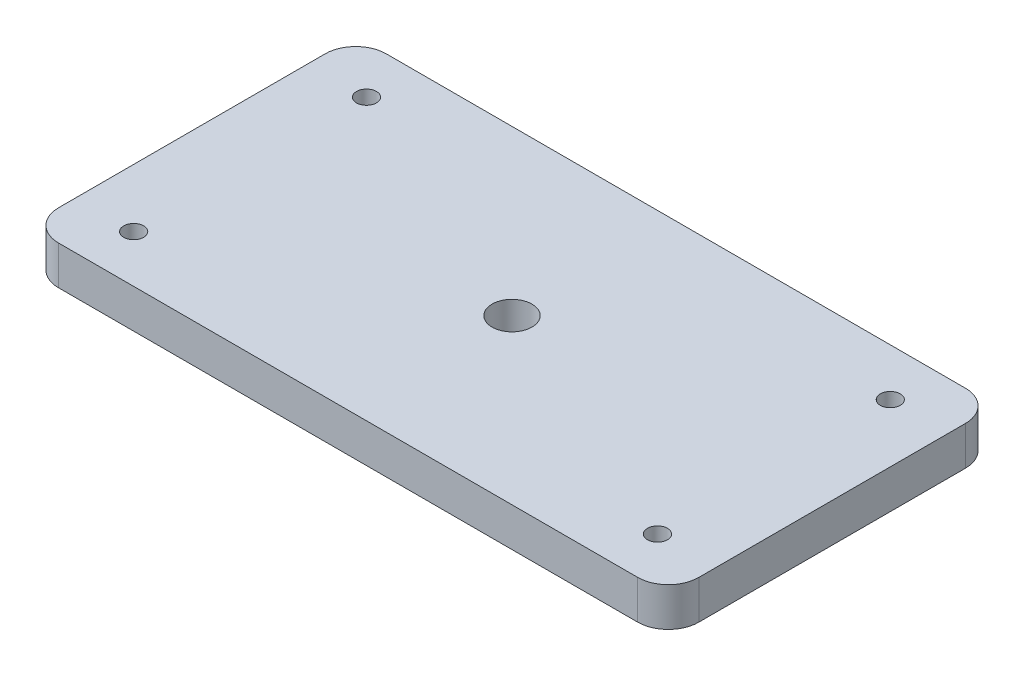
SolidWorks part; units mm, degrees
ref_plane "Front Plane" through (0, 0, 0) normal (0, 0, 1) x (1, 0, 0)
ref_plane "Top Plane" through (0, 0, 0) normal (0, 1, 0) x (1, 0, 0)
ref_plane "Right Plane" through (0, 0, 0) normal (1, 0, 0) x (0, 0, -1)
sketch "Sketch1" plane through (0, 0, 0) normal (0, 1, 0) x (1, 0, 0)
  line L1 (0, 53.63) -> (104.78, 53.63)
  line L2 (0, 53.63) -> (0, 0)
  line L3 (0, 0) -> (104.78, 0)
  line L4 (104.78, 53.63) -> (104.78, 0)
  dimension "dim1" = 104.78
  dimension "dim2" = 53.63
extrude "Boss-Extrude1" add sketch "Sketch1" along normal blind 6.35
sketch "Sketch3" plane through (0, 0, 0) normal (0, -1, 0) x (1, 0, 0)
  line L0 (104.78, 0) -> (104.78, -53.63) construction
  line L1 (0, 0) -> (104.78, 0) construction
  point P0 (52.39, -26.815)
  dimension "D1" = 52.39
  dimension "D2" = 26.815
hole_wizard "F (0.257) Diameter Hole1" positions "Sketch4" profile "Sketch5" hole size "F" standard "ANSI Inch" end condition through all
sketch "Sketch4" plane through (0, 0, 0) normal (0, -1, 0) x (-1, 0, 0)
  point P0 (-52.39, 26.815)
sketch "Sketch5" plane through (52.39, 0, -26.815) normal (1, 0, 0) x (0, 0, -1)
  line L0 (0, 0) -> (0, 6.35)
  line L1 (0, 6.35) -> (3.2639, 6.35)
  line L2 (3.2639, 6.35) -> (3.2639, 0)
  line L5 (3.2639, 0) -> (0, 0)
  line L11 (0, -6.35) -> (0, 107.95) construction
  dimension "Thru Hole Dia." = 6.5278
  dimension "Thru Hole Depth" = 6.35
sketch "Sketch6" plane through (0, 0, 0) normal (0, -1, 0) x (1, 0, 0)
  circle A0 centre (95.25, -7.765) radius 1.4224
  circle A1 centre (95.25, -7.765) radius 1.4224
  circle A2 centre (9.525, -7.765) radius 1.4224
  circle A3 centre (9.525, -7.765) radius 1.4224
  circle A4 centre (95.25, -45.865) radius 1.4224
  circle A5 centre (95.25, -45.865) radius 1.4224
  circle A6 centre (9.525, -45.865) radius 1.4224
  circle A7 centre (9.525, -45.865) radius 1.4224
hole_wizard "#30 (0.1285) Diameter Hole1" positions "Sketch7" profile "Sketch8" hole size "#30" standard "ANSI Inch" end condition through all
sketch "Sketch7" plane through (0, 0, 0) normal (0, -1, 0) x (-1, 0, 0)
  point P0 (-9.525, 7.765)
  point P3 (-9.525, 45.865)
  point P6 (-95.25, 45.865)
  point P9 (-95.25, 7.765)
sketch "Sketch8" plane through (9.525, 0, -7.765) normal (1, 0, 0) x (0, 0, -1)
  line L0 (0, 0) -> (0, 6.35)
  line L1 (0, 6.35) -> (1.6319, 6.35)
  line L2 (1.6319, 6.35) -> (1.6319, 0)
  line L5 (1.6319, 0) -> (0, 0)
  line L11 (0, -6.35) -> (0, 107.95) construction
  dimension "Thru Hole Dia." = 3.2639
  dimension "Thru Hole Depth" = 6.35
fillet "Fillet1" radius 5 4 edges at (0, 3.175, -53.63) (104.78, 3.175, -53.63) (104.78, 3.175, 0) (0, 3.175, 0)
